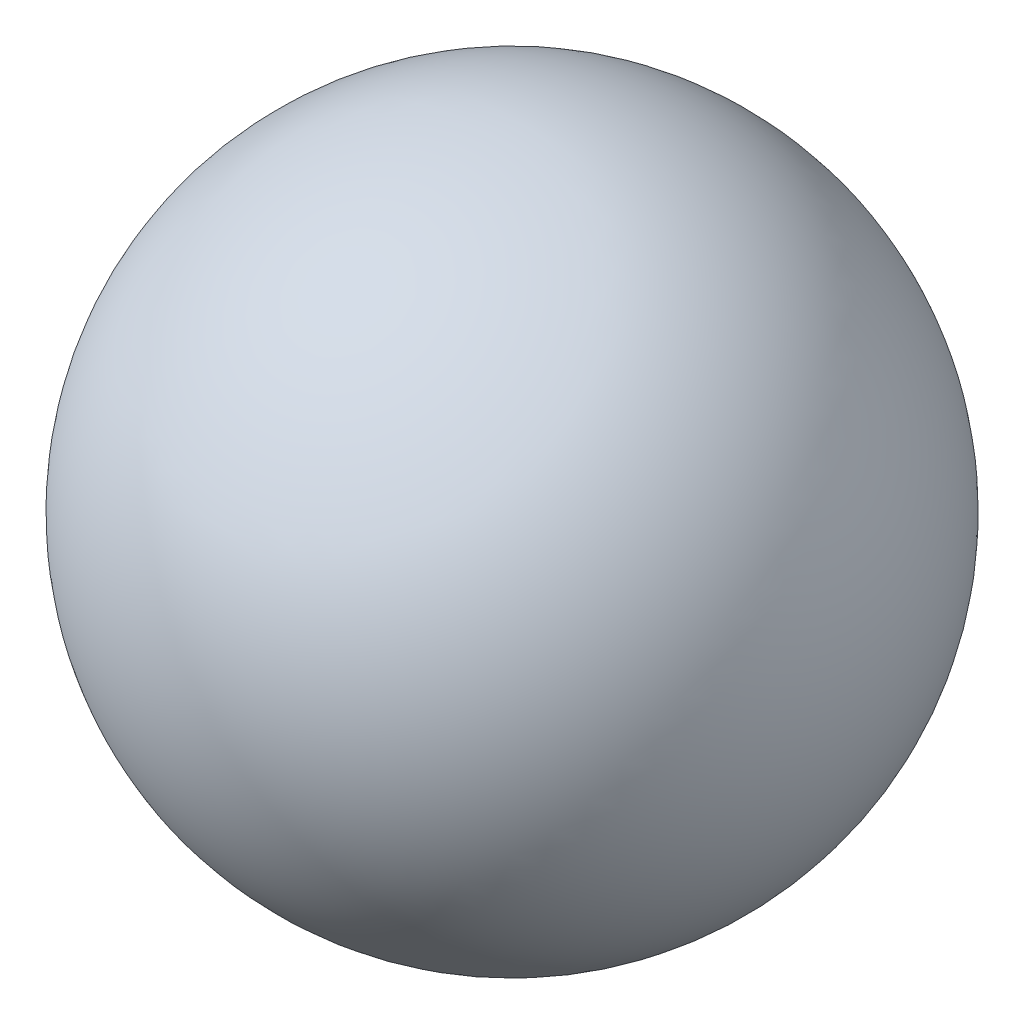
SolidWorks part; units mm, degrees
ref_plane "Front Plane" through (0, 0, 0) normal (0, 0, 1) x (1, 0, 0)
ref_plane "Top Plane" through (0, 0, 0) normal (0, 1, 0) x (1, 0, 0)
ref_plane "Right Plane" through (0, 0, 0) normal (1, 0, 0) x (0, 0, -1)
sketch "Sketch1" plane through (0, 0, 0) normal (0, 1, 0) x (1, 0, 0)
  line L0 (81.0484, -18.0448) -> (81.0484, 111.9552)
  circle A0 centre (81.0484, 46.9552) radius 65
revolve "Revolve1" add sketch "Sketch1" angle 360 about L0
